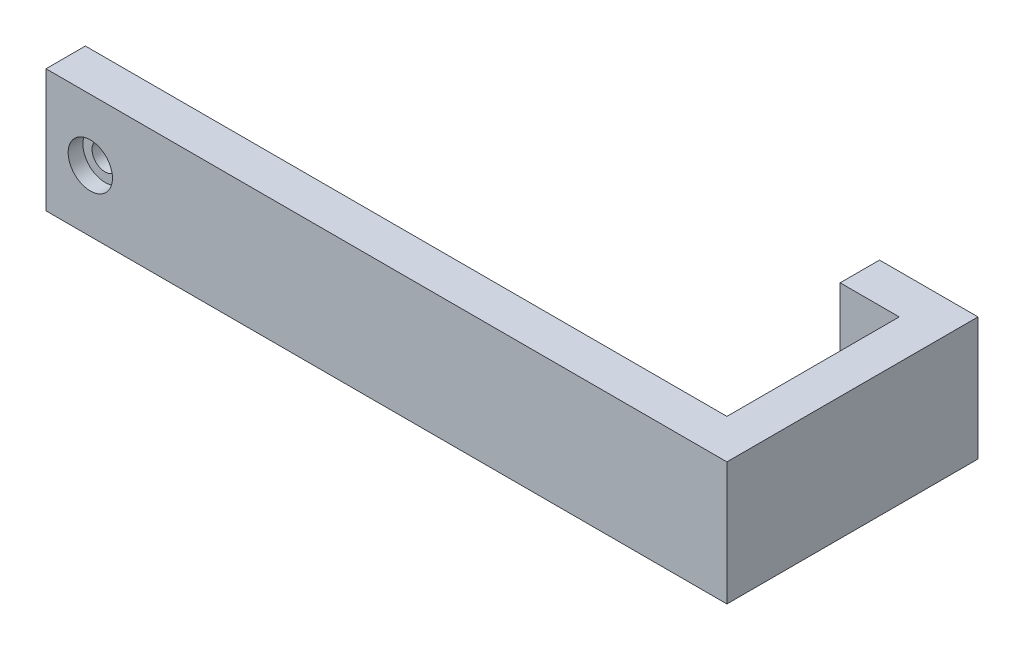
SolidWorks part; units mm, degrees
other "标注1"
sketch "草图6" plane through (33.7072, 1.196, 0) normal (0.6738, 0.696, -0.2482) x (0.0131, -0.347, -0.9378)
ref_plane "前视基准面" through (0, 0, 0) normal (0, 0, 1) x (1, 0, 0)
ref_plane "上视基准面" through (0, 0, 0) normal (0, 1, 0) x (1, 0, 0)
ref_plane "右视基准面" through (0, 0, 0) normal (1, 0, 0) x (0, 0, -1)
other "Configuration Table"
sketch "草图1" plane through (0, 0, 0) normal (0, 0, 1) x (1, 0, 0)
  line L22 (-8, 12.5) -> (129.3, 12.5)
  line L24 (-8, -12.5) -> (129.3, -12.5)
  line L25 (129.3, -12.5) -> (129.3, 12.5)
  line L26 (-8, 12.5) -> (-9, 12.5)
  line L27 (-9, 12.5) -> (-9, -12.5)
  line L28 (-9, -12.5) -> (-8, -12.5)
  circle A0 centre (0, 0) radius 2.65
  point P0 (0, 0)
extrude "凸台-拉伸1" add sketch "草图1" along normal blind 8
sketch "草图7" plane through (0, 0, 0) normal (0, 0, -1) x (-1, 0, 0)
  line L0 (-129.3, 12.5) -> (-121.3, 12.5)
  line L1 (8, 12.5) -> (-129.3, 12.5) construction
  line L2 (-129.3, 12.5) -> (-129.3, -12.5)
  line L3 (-129.3, -12.5) -> (-121.3, -12.5)
  line L4 (8, -12.5) -> (-129.3, -12.5) construction
  line L5 (-121.3, -12.5) -> (-121.3, 12.5)
extrude "凸台-拉伸2" add sketch "草图7" along normal blind 43
sketch "草图8" plane through (121.3, 0, 0) normal (-1, 0, 0) x (0, 0, 1)
  line L0 (-43, 12.5) -> (-35, 12.5)
  line L1 (-43, 12.5) -> (0, 12.5) construction
  line L2 (-35, 12.5) -> (-35, -12.5)
  line L3 (-43, -12.5) -> (0, -12.5) construction
  line L4 (-43, 12.5) -> (-43, -12.5)
  line L5 (-35, -12.5) -> (-43, -12.5)
extrude "凸台-拉伸3" add sketch "草图8" along normal blind 12
sketch "草图9" plane through (0, 0, 8) normal (0, 0, 1) x (1, 0, 0)
  circle A0 centre (0, 0) radius 4.5
extrude "切除-拉伸1" cut sketch "草图9" against normal blind 3
